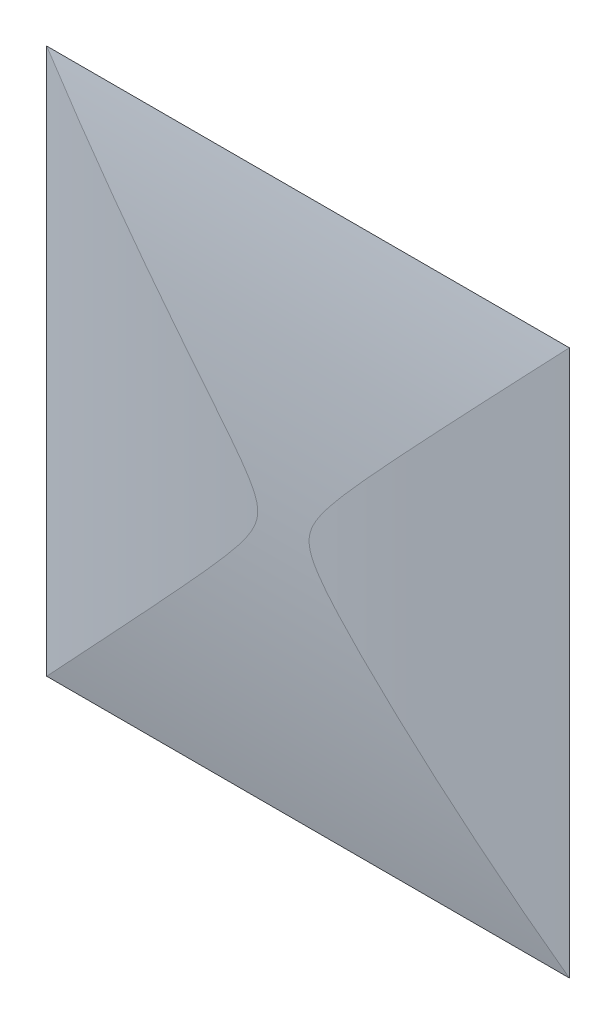
SolidWorks part; units mm, degrees
ref_plane "Front" through (0, 0, 0) normal (0, 0, 1) x (1, 0, 0)
ref_plane "Top" through (0, 0, 0) normal (0, 1, 0) x (1, 0, 0)
ref_plane "Right" through (0, 0, 0) normal (1, 0, 0) x (0, 0, -1)
sketch "Sketch1" plane through (0, 0, 0) normal (0, 0, 1) x (1, 0, 0)
  line L0 (-5.65, 0) -> (5.65, 0) construction
  line L1 (-5.65, 5.9) -> (5.65, 5.9)
  line L2 (-5.65, 5.9) -> (-5.65, -5.9)
  line L3 (-5.65, -5.9) -> (5.65, -5.9)
  line L4 (5.65, 5.9) -> (5.65, -5.9)
  point P6 (0, 0)
  dimension "D1" = 11.3
  dimension "D2" = 11.8
extrude "key" add sketch "Sketch1" along normal blind 1
sketch "Sketch2" plane through (0, -5.9, 0) normal (0, -1, 0) x (1, 0, 0)
  line L0 (-5.65, 1) -> (-5.65, 0) construction
  line L1 (-5.65, 0) -> (-5.65, 1)
  line L2 (-5.65, 1) -> (5.65, 1)
  line L3 (5.65, 1) -> (5.65, 0)
  arc A0 (5.65, 0) -> (-5.65, 0) centre (0, -29.4632) ccw
  dimension "D1" = 30
extrude "Extrude2" cut sketch "Sketch2" against normal through all
sketch "Croquis1" plane through (0, 0, 0) normal (1, 0, 0) x (0, 0, -1)
  line L0 (0, -5.9) -> (0, 5.9) construction
  line L1 (0, 5.9) -> (-1.526, 5.9)
  line L2 (-1.526, 5.9) -> (-1.526, -5.9)
  line L3 (-1.526, -5.9) -> (0, -5.9)
  arc A0 (0, 5.9) -> (0, -5.9) centre (32.4683, 0) ccw
  dimension "D1" = 33
extrude "Cortar-Extruir2" cut sketch "Croquis1" against normal through all both and the other way through all
